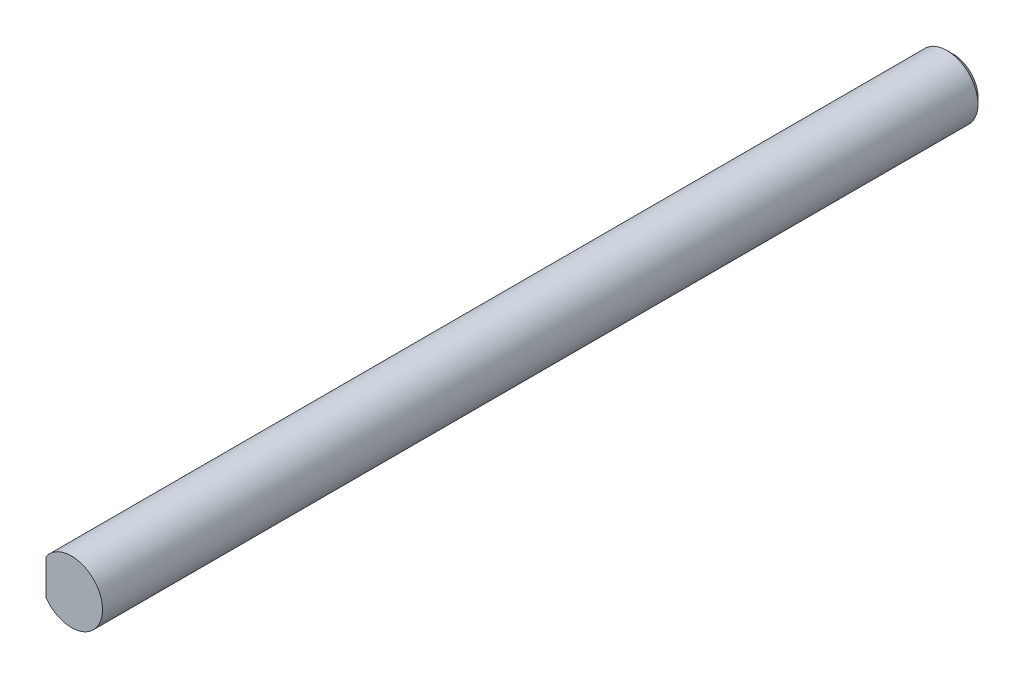
SolidWorks part; units mm, degrees
material "Acero aleado"
ref_plane "Alzado" through (0, 0, 0) normal (0, 0, 1) x (1, 0, 0)
ref_plane "Planta" through (0, 0, 0) normal (0, 1, 0) x (1, 0, 0)
ref_plane "Vista lateral" through (0, 0, 0) normal (1, 0, 0) x (0, 0, -1)
sketch "Croquis1" plane through (0, 0, 0) normal (0, 0, 1) x (1, 0, 0)
  circle A0 centre (0, 0) radius 2.5
  dimension "D1" = 5
extrude "Saliente-Extruir1" add sketch "Croquis1" along normal blind 71
sketch "Sketch1" plane through (0, 0, 71) normal (0, 0, 1) x (1, 0, 0)
  line L0 (-2.05, 1.4309) -> (-2.05, -1.4309)
  line L1 (-2.05, 0) -> (2.5, 0) construction
  arc A2 (-2.05, 1.4309) -> (-2.05, -1.4309) centre (0, 0) ccw
  circle A3 centre (0, 0) radius 2.5 construction
  dimension "D1" = 4.55
extrude "Cut-Extrude1" cut sketch "Sketch1" against normal blind 14
chamfer "Chamfer1" distance 0.5 angle 45 1 edges at (2.5, 0, 0)
